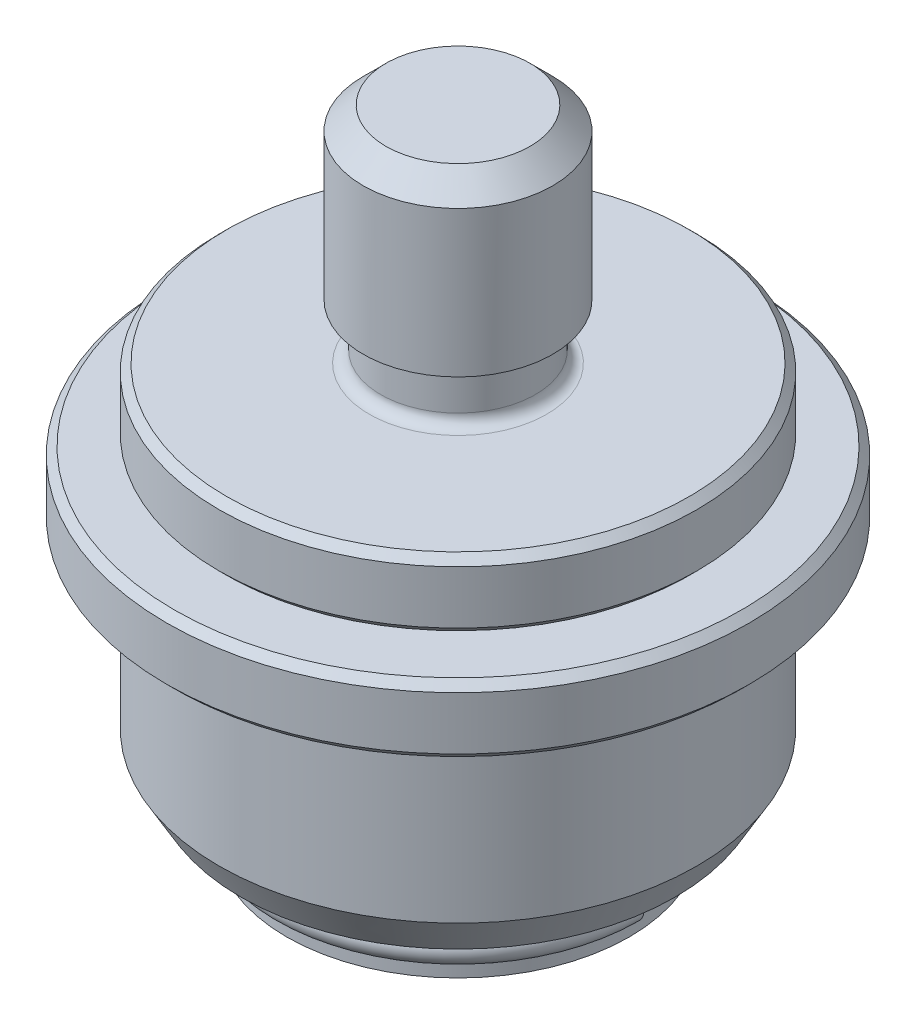
SolidWorks part; units mm, degrees
ref_plane "Front Plane" through (0, 0, 0) normal (0, 0, 1) x (1, 0, 0)
ref_plane "Top Plane" through (0, 0, 0) normal (0, 1, 0) x (1, 0, 0)
ref_plane "Right Plane" through (0, 0, 0) normal (1, 0, 0) x (0, 0, -1)
sketch "Sketch1" plane through (0, 0, 0) normal (0, 0, 1) x (1, 0, 0)
  line L0 (0, 14.986) -> (0, -15.5321)
  line L1 (0, 14.986) -> (6.35, 14.986)
  line L2 (6.35, 14.986) -> (6.35, 3.683)
  line L3 (5.9436, 0) -> (16.002, 0)
  line L4 (16.002, 0) -> (16.002, -4.572)
  line L5 (16.002, -4.572) -> (11.4808, -4.572)
  line L6 (11.4808, -4.572) -> (11.4808, -24.5618)
  line L7 (11.4808, -27.559) -> (9.5504, -27.559)
  line L8 (0, 14.986) -> (0, 50.8132) construction
  line L9 (6.35, 3.683) -> (5.1816, 3.683)
  line L10 (5.1816, 3.683) -> (5.1816, 0.762)
  line L11 (8.0264, -26.035) -> (8.0264, -20.066)
  line L12 (8.0264, -20.066) -> (3.4925, -15.5321)
  line L13 (3.4925, -15.5321) -> (0, -15.5321)
  line L14 (11.4808, -26.5938) -> (11.4808, -27.559)
  arc A0 (11.4808, -24.5618) -> (11.4808, -26.5938) centre (11.4808, -25.5778) ccw
  arc A1 (9.5504, -27.559) -> (8.0264, -26.035) centre (9.5504, -26.035) cw
  arc A2 (5.9436, 0) -> (5.1816, 0.762) centre (5.9436, 0.762) cw
  dimension "D14" = 1.016
  dimension "D15" = 1.524
  dimension "D16" = 0.762
  dimension "D1" = 12.7
  dimension "D2" = 14.986
  dimension "D3" = 4.572
  dimension "D4" = 27.559
  dimension "D5" = 22.9616
  dimension "D6" = 32.004
  dimension "D7" = 3.683
  dimension "D8" = 10.3632
  dimension "D9" = 16.0528
  dimension "D10" = 7.493
  dimension "D11" = 45
  dimension "D12" = 6.985
  dimension "D13" = 0.9652
revolve "Revolve1" add sketch "Sketch1" angle 360 about L8
chamfer "Chamfer1" distance 0.508 angle 45 2 edges at (0, -4.572, -16.002) (0, 0, -16.002)
chamfer "Chamfer2" distance 1.524 angle 45 1 edges at (0, 14.986, -6.35)
sketch "Sketch2" plane through (0, 0, 0) normal (0, 0, 1) x (1, 0, 0)
  line L0 (11.5316, -4.826) -> (11.5316, -20.7264)
  line L1 (13.208, -23.7236) -> (14.5355, -23.7236)
  line L2 (14.5355, -23.7236) -> (16.002, -21.1836)
  line L3 (16.002, -21.1836) -> (16.002, -10.16)
  line L4 (16.764, -9.398) -> (19.5072, -9.398)
  line L5 (19.5072, -9.398) -> (19.5072, -4.826)
  line L6 (19.5072, -4.826) -> (11.5316, -4.826)
  line L7 (0, 0) -> (0, 33.0062) construction
  line L8 (15.494, 0) -> (-15.494, 0) construction
  line L9 (11.4808, -24.5618) -> (11.4808, -4.572) construction
  line L11 (13.208, -23.7236) -> (13.208, -21.7424)
  line L12 (12.192, -20.7264) -> (11.5316, -20.7264)
  line L13 (11.4808, -24.5618) -> (-11.4808, -24.5618) construction
  line L14 (-11.4808, -27.559) -> (11.4808, -27.559) construction
  arc A0 (13.208, -21.7424) -> (12.192, -20.7264) centre (12.192, -21.7424) ccw
  arc A1 (16.002, -10.16) -> (16.764, -9.398) centre (16.764, -10.16) cw
  dimension "D13" = 1.016
  dimension "D14" = 0.762
  dimension "D1" = 18.8976
  dimension "D2" = 4.572
  dimension "D3" = 32.004
  dimension "D4" = 39.0144
  dimension "D5" = 2.54
  dimension "D6" = 30
  dimension "D7" = 29.0711
  dimension "D8" = 9.398
  dimension "D9" = 0.0508
  dimension "D10" = 3.8354
  dimension "D11" = 3.8354
  dimension "D12" = 26.416
revolve "Revolve2" add sketch "Sketch2" angle 360 about L7
chamfer "Chamfer3" distance 0.508 angle 45 2 edges at (0, -4.826, -19.5072) (0, -9.398, -19.5072)
sketch "Sketch3" plane through (0, 0, 0) normal (0, 0, 1) x (1, 0, 0)
  line L1 (0, 0) -> (0, -31.4929) construction
  circle A0 centre (11.4808, -25.5778) radius 0.9652
  arc A2 (11.4808, -24.5618) -> (11.4808, -26.5938) centre (11.4808, -25.5778) ccw construction
  dimension "D1" = 0.0508
revolve "Revolve3" add sketch "Sketch3" angle 315 about L1
